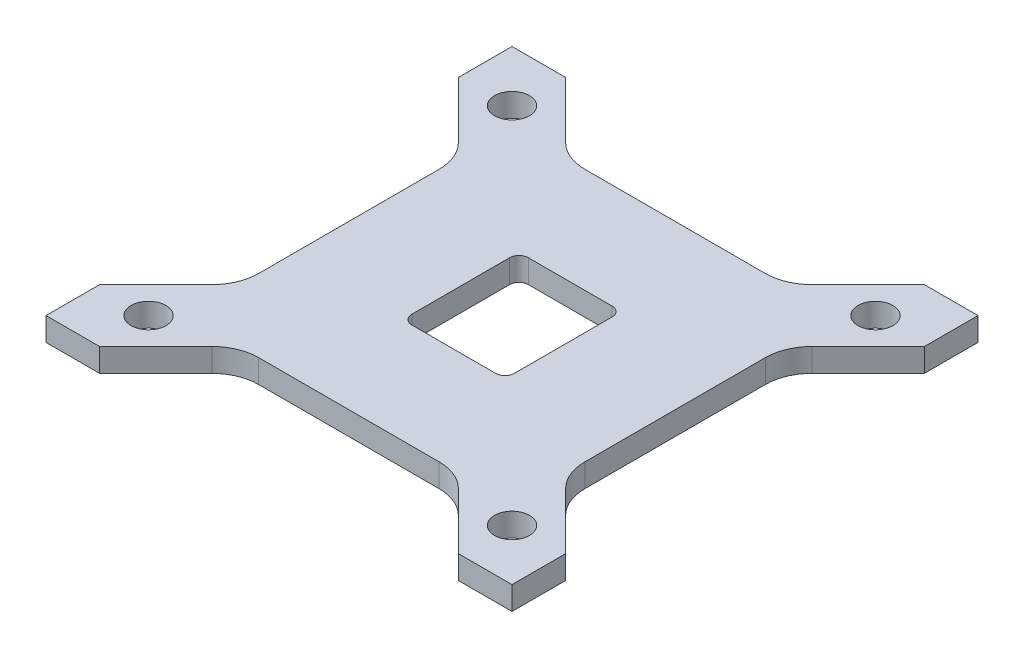
SolidWorks part; units mm, degrees
ref_plane "正面" through (0, 0, 0) normal (0, 0, 1) x (1, 0, 0)
ref_plane "平面" through (0, 0, 0) normal (0, 1, 0) x (1, 0, 0)
ref_plane "右側面" through (0, 0, 0) normal (1, 0, 0) x (0, 0, -1)
sketch "ｽｹｯﾁ1" plane through (0, 0, 0) normal (0, 1, 0) x (1, 0, 0)
  line L0 (-50, 38.5) -> (-50, 50)
  line L5 (-50, 50) -> (50, -50) construction
  line L6 (-50, -50) -> (50, 50) construction
  line L7 (38.5, 50) -> (50, 50)
  line L8 (-50, 38.5) -> (-35, 23.5)
  line L9 (-35, 23.5) -> (-35, -23.5)
  line L10 (-35, -23.5) -> (-50, -38.5)
  line L11 (-50, -38.5) -> (-50, -50)
  line L12 (38.5, 50) -> (23.5, 35)
  line L13 (23.5, 35) -> (-23.5, 35)
  line L14 (-23.5, 35) -> (-38.5, 50)
  line L15 (-38.5, 50) -> (-50, 50)
  line L16 (50, -38.5) -> (50, -50)
  line L17 (50, -38.5) -> (35, -23.5)
  line L18 (35, -23.5) -> (35, 23.5)
  line L19 (35, 23.5) -> (50, 38.5)
  line L20 (50, 38.5) -> (50, 50)
  line L21 (-38.5, -50) -> (-50, -50)
  line L22 (-38.5, -50) -> (-23.5, -35)
  line L23 (-23.5, -35) -> (23.5, -35)
  line L24 (23.5, -35) -> (38.5, -50)
  line L25 (38.5, -50) -> (50, -50)
  point P0 (0, 0)
  point P31 (0, 0)
  dimension "D1" = 100
  dimension "D2" = 100
  dimension "D3" = 11.5
  dimension "D4" = 135
  dimension "D5" = 15
  dimension "D6" = 4
extrude "ﾎﾞｽ - 押し出し1" add sketch "ｽｹｯﾁ1" along normal blind 5
sketch "ｽｹｯﾁ2" plane through (0, 5, 0) normal (0, 1, 0) x (1, 0, 0)
  line L0 (-50, 50) -> (50, -50) construction
  line L1 (-50, -50) -> (50, 50) construction
  line L2 (-55, 0) -> (55, 0) construction
  circle A0 centre (-39, 39) radius 3.75
  circle A1 centre (39, 39) radius 3.75
  circle A2 centre (39, -39) radius 3.75
  circle A3 centre (-39, -39) radius 3.75
  point P12 (0, 0)
  dimension "D1" = 7.5
  dimension "D2" = 78
extrude "ｶｯﾄ - 押し出し1" cut sketch "ｽｹｯﾁ2" against normal through all
fillet "ﾌｨﾚｯﾄ1" radius 10 8 edges at (-23.5, 2.5, -35) (23.5, 2.5, -35) (35, 2.5, -23.5) (35, 2.5, 23.5) (23.5, 2.5, 35) (-23.5, 2.5, 35) (-35, 2.5, 23.5) (-35, 2.5, -23.5)
sketch "ｽｹｯﾁ3" plane through (0, 5, 0) normal (0, 1, 0) x (1, 0, 0)
  line L1 (-11, 12.5) -> (11, 12.5)
  line L2 (-11, 12.5) -> (-11, -12.5)
  line L3 (-11, -12.5) -> (11, -12.5)
  line L4 (11, 12.5) -> (11, -12.5)
  line L5 (-11, 12.5) -> (11, -12.5) construction
  line L6 (-11, -12.5) -> (11, 12.5) construction
  point P0 (0, 0)
  dimension "D1" = 22
  dimension "D2" = 25
extrude "ｶｯﾄ - 押し出し2" cut sketch "ｽｹｯﾁ3" against normal through all
fillet "ﾌｨﾚｯﾄ2" radius 2 4 edges at (11, 2.5, 12.5) (-11, 2.5, 12.5) (11, 2.5, -12.5) (-11, 2.5, -12.5)
